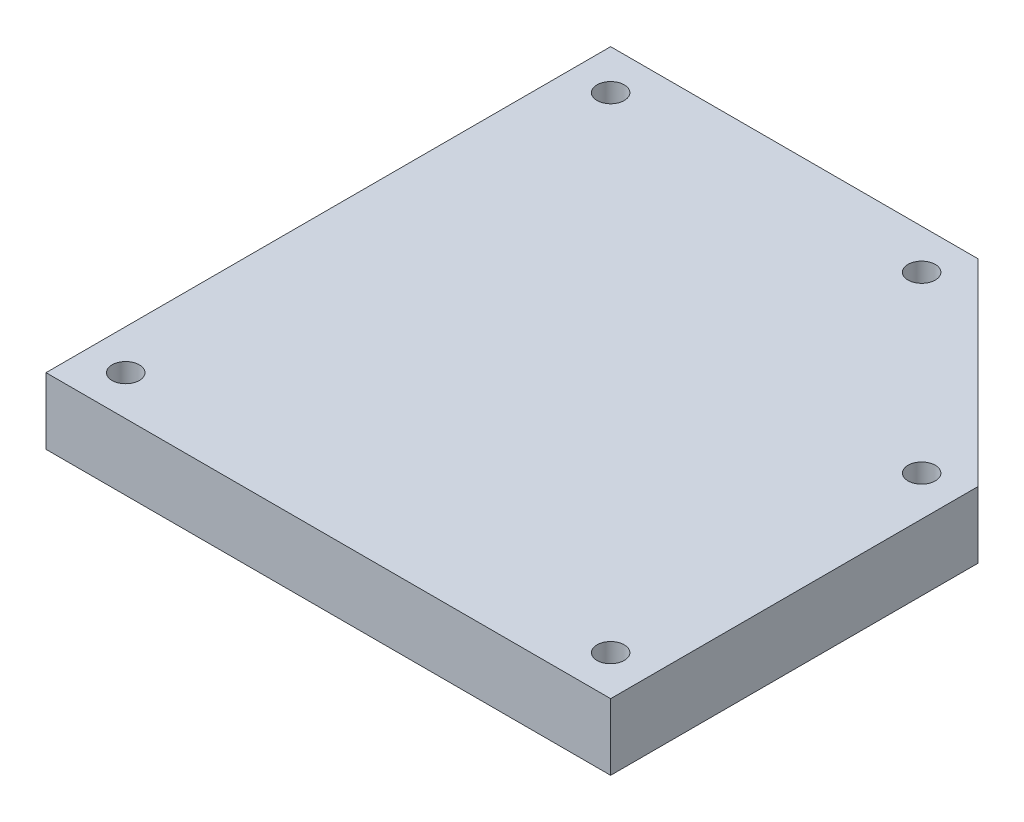
SolidWorks part; units mm, degrees
ref_plane "Front Plane" through (0, 0, 0) normal (0, 0, 1) x (1, 0, 0)
ref_plane "Top Plane" through (0, 0, 0) normal (0, 1, 0) x (1, 0, 0)
ref_plane "Right Plane" through (0, 0, 0) normal (1, 0, 0) x (0, 0, -1)
sketch "Sketch1" plane through (0, 0, 0) normal (0, 1, 0) x (1, 0, 0)
  line L0 (-41.1601, 19.7961) -> (-41.1601, -65.2039)
  line L1 (-41.1601, -65.2039) -> (43.8399, -65.2039)
  line L2 (43.8399, -65.2039) -> (43.8399, -9.9024)
  line L3 (43.8399, -9.9024) -> (14.1414, 19.7961)
  line L4 (14.1414, 19.7961) -> (-41.1601, 19.7961)
  dimension "D1" = 85
  dimension "D2" = 85
  dimension "D3" = 42
  dimension "D4" = 135
extrude "Boss-Extrude1" add sketch "Sketch1" along normal blind 10
sketch "Sketch2" plane through (0, 10, 0) normal (0, 1, 0) x (1, 0, 0)
  line L0 (43.8399, -65.2039) -> (43.8399, -9.9024) construction
  line L1 (43.8399, -9.9024) -> (14.1414, 19.7961) construction
  line L2 (-41.1601, -65.2039) -> (43.8399, -65.2039) construction
  line L3 (-41.1601, 19.7961) -> (-41.1601, -65.2039) construction
  line L4 (14.1414, 19.7961) -> (-41.1601, 19.7961) construction
  circle A0 centre (37.8399, -12.3877) radius 2.05
  circle A1 centre (37.8399, -59.2039) radius 2.05
  circle A2 centre (-35.1601, -59.2039) radius 2.05
  circle A3 centre (-35.1601, 13.7961) radius 2.05
  circle A4 centre (11.6561, 13.7961) radius 2.05
  dimension "D1" = 6
  dimension "D2" = 6
  dimension "D3" = 6
  dimension "D4" = 6
  dimension "D5" = 6
  dimension "D6" = 6
  dimension "D7" = 6
  dimension "D8" = 6
  dimension "D9" = 6
  dimension "D10" = 6
  dimension "D11" = 4.1
  dimension "D12" = 4.1
  dimension "D13" = 4.1
  dimension "D14" = 4.1
  dimension "D15" = 4.1
extrude "Cut-Extrude3" cut sketch "Sketch2" against normal up to next
sketch "Sketch5" plane through (0, 0, 0) normal (0, -1, 0) x (1, 0, 0)
  circle A0 centre (37.8399, 59.2039) radius 4
  circle A1 centre (37.8399, 12.3877) radius 4
  circle A2 centre (11.6561, -13.7961) radius 4
  circle A3 centre (-35.1601, -13.7961) radius 4
  circle A4 centre (-35.1601, 59.2039) radius 4
  dimension "D1" = 8
  dimension "D2" = 8
  dimension "D3" = 8
  dimension "D4" = 8
  dimension "D5" = 8
extrude "Cut-Extrude4" cut sketch "Sketch5" against normal blind 5
